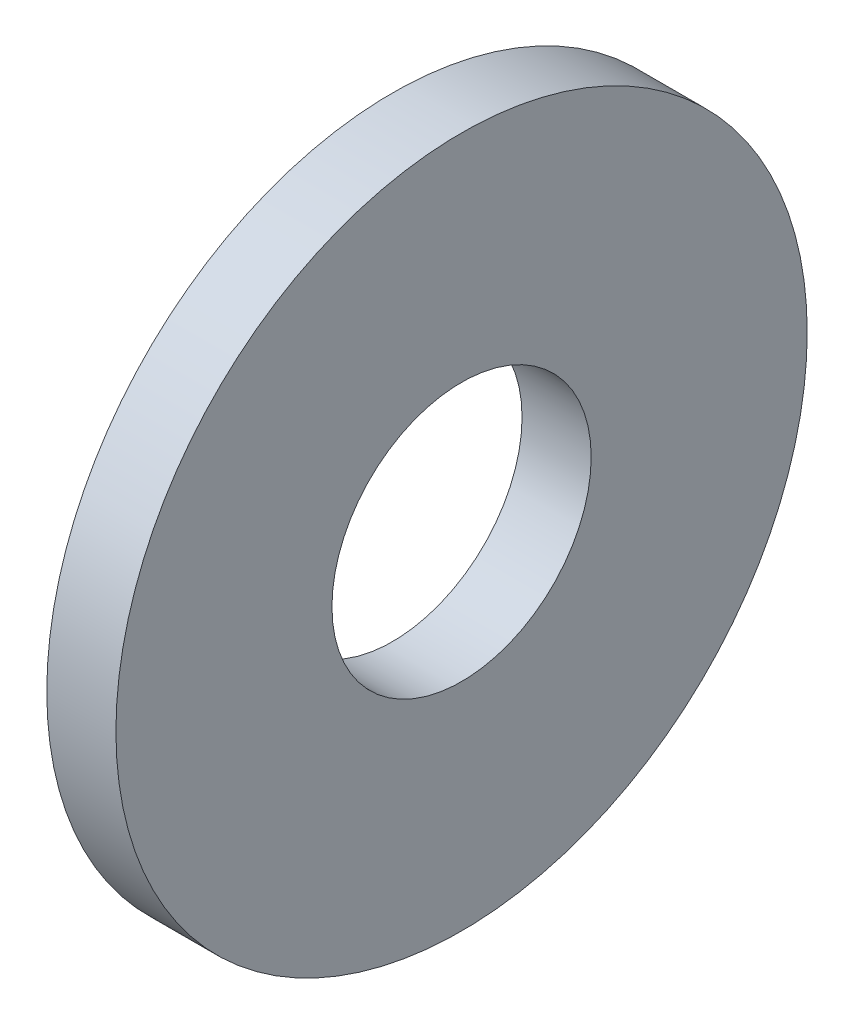
SolidWorks part; units mm, degrees
ref_plane "Plane1" through (0, 0, 0) normal (0, 0, 1) x (1, 0, 0)
ref_plane "Plane2" through (0, 0, 0) normal (0, 1, 0) x (1, 0, 0)
ref_plane "Plane3" through (0, 0, 0) normal (1, 0, 0) x (0, 0, -1)
sketch "Sketch1" plane through (0, 0, 0) normal (1, 0, 0) x (0, 0, -1)
  circle A0 centre (0, 0) radius 1.125
  circle A1 centre (0, 0) radius 3
  dimension "Insid_dia" = 2.25
  dimension "OutsideDia" = 6
extrude "Base-Extrude" add sketch "Sketch1" along normal blind 0.6
